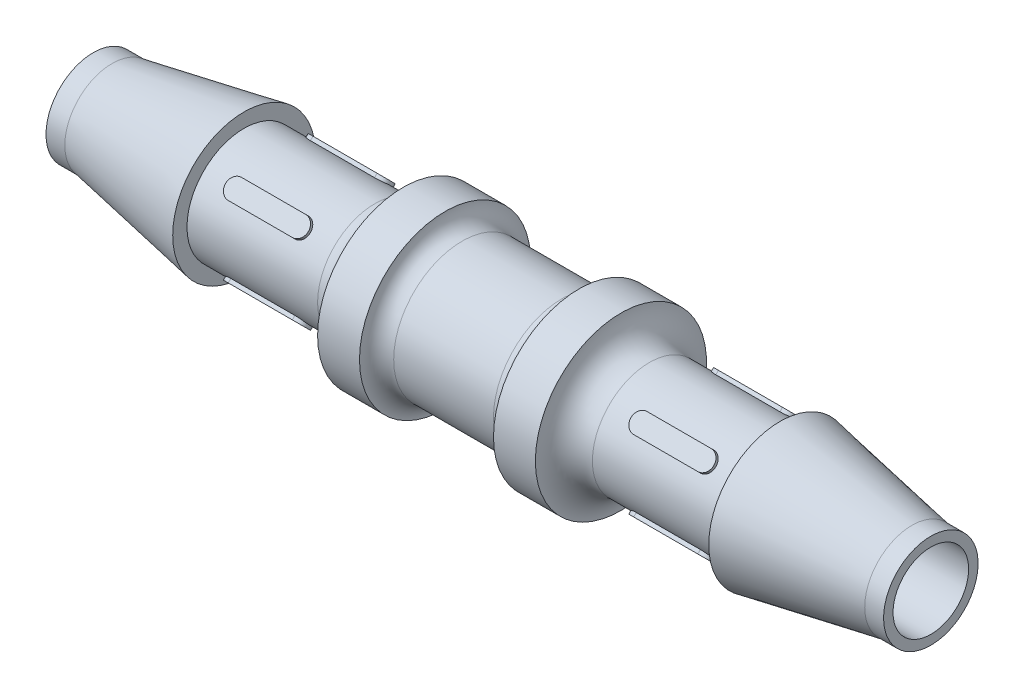
SolidWorks part; units mm, degrees
ref_plane "Front Plane" through (0, 0, 0) normal (0, 0, 1) x (1, 0, 0)
ref_plane "Top Plane" through (0, 0, 0) normal (0, 1, 0) x (1, 0, 0)
ref_plane "Right Plane" through (0, 0, 0) normal (1, 0, 0) x (0, 0, -1)
sketch "Sketch1" plane through (0, 0, 0) normal (0, 0, 1) x (1, 0, 0)
  line L0 (0, 0) -> (23.495, 0) construction
  line L1 (23.495, 2.1209) -> (23.495, 2.6511)
  line L3 (15.0368, 4.0005) -> (15.0368, 3.2004)
  line L4 (15.0368, 3.2004) -> (6.1087, 3.2004)
  line L5 (23.495, 2.6511) -> (22.4377, 2.6511)
  line L6 (6.1087, 3.2004) -> (6.1087, 4.8006)
  line L7 (6.1087, 4.8006) -> (3.7592, 4.8006)
  line L8 (3.7592, 4.8006) -> (3.7592, 3.8405)
  line L9 (3.7592, 3.8405) -> (0, 3.8405)
  line L10 (23.495, 2.1209) -> (0, 2.1209)
  line L11 (0, 2.1209) -> (0, 3.8405)
  line L12 (9.0221, 3.6004) -> (15.0368, 3.6004) construction
  line L13 (0, 0) -> (0, -2.6412) construction
  line L14 (22.4377, 2.6511) -> (15.0368, 4.0005)
  dimension "D1" = 5.3023
  dimension "C" = 46.99
  dimension "A" = 4.2418
  dimension "B" = 8.001
  dimension "D2" = 6.4008
  dimension "D3" = 8.4582
  dimension "D4" = 2.3495
  dimension "D5" = 9.6012
  dimension "D6" = 3.7592
  dimension "D7" = 7.681
  dimension "D8" = 1.0573
revolve "Revolve1" add sketch "Sketch1" angle 360 about L0
sketch "Sketch2" plane through (0, 0, 0) normal (0, 0, 1) x (1, 0, 0)
  line L0 (15.0368, 3.2004) -> (6.1087, 3.2004) construction
  line L1 (6.1087, 3.2004) -> (6.1087, 4.8006) construction
  line L2 (7.7089, 3.2004) -> (6.1087, 3.2004)
  line L3 (6.1087, 3.2004) -> (6.1087, 4.8006)
  line L4 (3.7592, 4.8006) -> (3.7592, 3.8405) construction
  line L5 (3.7592, 3.8405) -> (0, 3.8405) construction
  line L6 (3.7592, 4.8006) -> (3.7592, 3.8405)
  line L7 (3.7592, 3.8405) -> (2.7991, 3.8405)
  arc A0 (6.1087, 4.8006) -> (7.7089, 3.2004) centre (7.7089, 4.8006) ccw
  arc A1 (3.7592, 4.8006) -> (2.7991, 3.8405) centre (2.7991, 4.8006) cw
revolve "Revolve2" add sketch "Sketch2" angle 360 about L0
ref_plane "Plane1" through (0, 0, 0) normal (0, 0.7071, 0.7071) x (-1, 0, 0)
sketch "Sketch3" plane through (0, 0, 0) normal (0, 0.7071, 0.7071) x (-1, 0, 0)
  line L0 (0, 0) -> (-23.495, 0) construction
  line L1 (-9.5755, 0.5286) -> (-13.1702, 0.5286)
  line L2 (-9.5755, 0.5286) -> (-9.5755, -0.5286) construction
  line L3 (-9.5755, -0.5286) -> (-13.1702, -0.5286)
  line L4 (-13.1702, 0.5286) -> (-13.1702, -0.5286) construction
  line L5 (-7.7089, 3.1148) -> (-7.7089, 5.1415) construction
  line L6 (-7.7089, 5.1415) -> (-15.0368, 5.1415) construction
  line L7 (-15.0368, 5.1415) -> (-15.0368, 3.1148) construction
  line L8 (-11.3729, 5.1415) -> (-11.3729, 0.5286) construction
  line L9 (-7.7089, 3.1148) -> (-9.0468, 3.1148) construction
  line L10 (-9.0468, 3.1148) -> (-9.0468, -0.5731) construction
  line L11 (-15.0368, 3.1148) -> (-13.6989, 3.1148) construction
  line L12 (-13.6989, 3.1148) -> (-13.6989, -0.5731) construction
  arc A0 (-13.1702, 0.5286) -> (-13.1702, -0.5286) centre (-13.1702, 0) ccw
  arc A1 (-9.5755, 0.5286) -> (-9.5755, -0.5286) centre (-9.5755, 0) cw
  dimension "D1" = 1.0573
  dimension "D2" = 4.652
extrude "Extrude1" add sketch "Sketch3" along normal mid plane 6.7208
pattern_circular "CirPattern1" count 2 every 90 about axis through (0, 0, 0) along (1, 0, 0) of "Extrude1"
sketch "Sketch4" plane through (23.495, 0, 0) normal (1, 0, 0) x (0, 0, -1)
  circle A0 centre (0, 0) radius 2.1209 construction
  circle A1 centre (0, 0) radius 2.1209
extrude "Cut-Extrude1" cut sketch "Sketch4" against normal through all
mirror "Mirror1" about plane through (0, 0, 0) normal (1, 0, 0) of bodies 110
equation "\"D1@Sketch1\" = \"A@Sketch1\"*1.25"
equation "\"D3@Sketch1\" = \"C@Sketch1\"*.18"
equation "\"D4@Sketch1\" = \"C@Sketch1\"*.05"
equation "\"D6@Sketch1\" = \"C@Sketch1\"*.160/2"
equation "\"D2@Sketch1\" = \"B@Sketch1\"*.8"
equation "\"D5@Sketch1\" = \"B@Sketch1\"*1.2"
equation "\"D7@Sketch1\" = \"D2@Sketch1\"*1.2"
equation "\"D8@Sketch1\" = \"D3@Sketch1\"/8"
equation "\"D1@Sketch3\" = \"D8@Sketch1\""
equation "\"D2@Sketch3\" = \"D3@Sketch1\"*.55"
equation "\"D1@Extrude1\" = \"D2@Sketch1\"*1.05"
